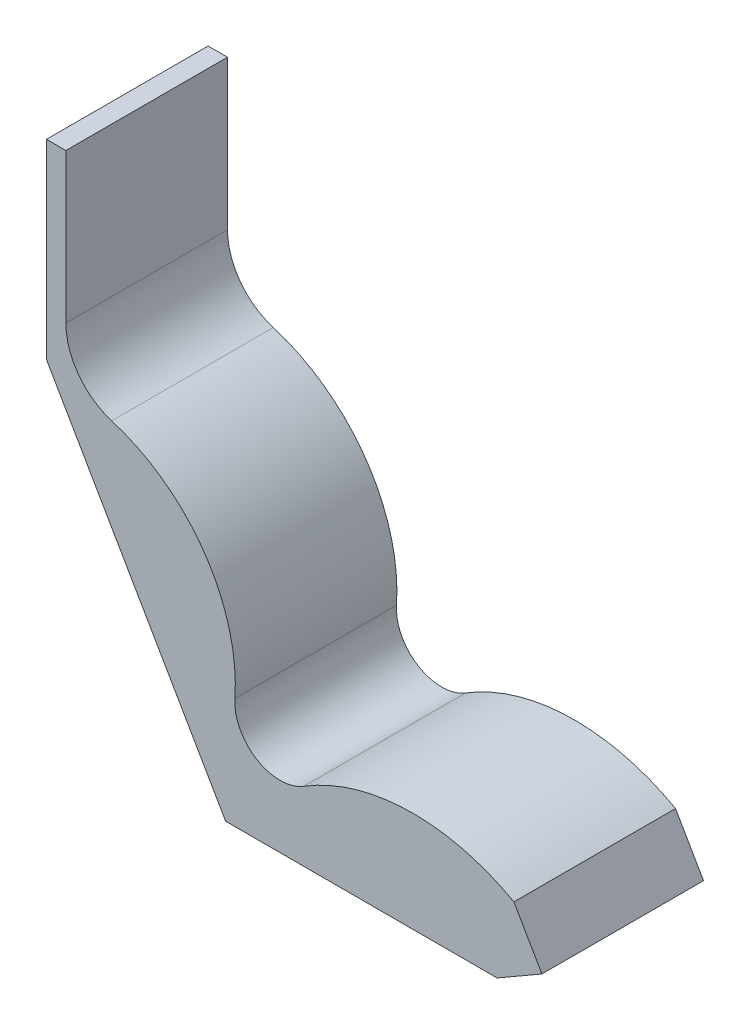
SolidWorks part; units mm, degrees
ref_plane "Front Plane" through (0, 0, 0) normal (0, 0, 1) x (1, 0, 0)
ref_plane "Top Plane" through (0, 0, 0) normal (0, 1, 0) x (1, 0, 0)
ref_plane "Right Plane" through (0, 0, 0) normal (1, 0, 0) x (0, 0, -1)
sketch "Sketch2" plane through (0, 0, 0) normal (0, 0, 1) x (1, 0, 0)
  line L0 (-277.1281, 480) -> (0, 0)
  line L1 (0, 0) -> (420, 0)
  line L2 (420, 0) -> (489.282, 40)
  line L3 (489.282, 40) -> (445.9808, 115)
  line L4 (-277.1281, 480) -> (-277.1281, 775)
  line L5 (-277.1281, 775) -> (-247.1281, 775)
  line L6 (-247.1281, 775) -> (-247.1281, 543.9261)
  arc A0 (445.9808, 115) -> (121.149, 107.4158) centre (290, -164.4101) ccw
  arc A1 (14.3749, 171.6382) -> (-176.2827, 448.2704) centre (-255, 190) ccw
  arc A2 (-176.2827, 448.2704) -> (-247.1281, 543.9261) centre (-147.1281, 543.9261) cw
  arc A3 (14.3749, 171.6382) -> (121.149, 107.4158) centre (84.2129, 166.8778) ccw
  dimension "D8" = 640
  dimension "D10" = 540
  dimension "D14" = 100
  dimension "D15" = 140
  dimension "D1" = 420
  dimension "D2" = 80
  dimension "D3" = 30
  dimension "D4" = 75
  dimension "D5" = 775
  dimension "D6" = 480
  dimension "D7" = 30
  dimension "D9" = 290
  dimension "D11" = 255
  dimension "D12" = 190
  dimension "D13" = 60
ref_plane "Plane1" through (-277.1281, 0, 0) normal (1, 0, 0) x (0, 1, 0)
ref_plane "Plane2" through (0, 0, 0) normal (-0.866, -0.5, 0) x (0.5, -0.866, 0)
ref_plane "Plane3" through (384.282, 221.8653, 0) normal (0.866, 0.5, 0) x (-0.5, 0.866, 0)
extrude "Boss-Extrude1" add sketch "Sketch2" along normal blind 250
sketch3d "3DSketch1"
  line L0 (-277.1281, 775, 0) -> (-277.1281, 775, 100)
  line L1 (-277.1281, 480, 0) -> (-277.1281, 480, 180)
  line L2 (-277.1281, 480, 0) -> (0, 0, 0) construction
  line L3 (0, 0, 0) -> (0, 0, 125)
  line L4 (420, 0, 0) -> (420, -7.5566, 199.8572)
  dimension "D1" = 100
  dimension "D2" = 180
  dimension "D3" = 125
  dimension "D4" = 200
sketch "Sketch3" plane through (-277.1281, 0, 0) normal (1, 0, 0) x (0, 1, 0)
  arc A0 (775, 100) -> (480, 180) centre (421.9698, -617.8925) ccw
  dimension "D1" = 800
sketch "Sketch4" plane through (0, 0, 0) normal (-0.866, -0.5, 0) x (0.5, -0.866, 0)
  arc A0 (-554.2563, 180) -> (0, 125) centre (-345.8935, -540.4755) cw
  dimension "D1" = 750
sketch "Sketch5" plane through (0, 0, 0) normal (0, 1, 0) x (1, 0, 0)
  arc A0 (0, -125) -> (420, -199.8572) centre (352.5601, 637.4312) ccw
  dimension "D1" = 840
